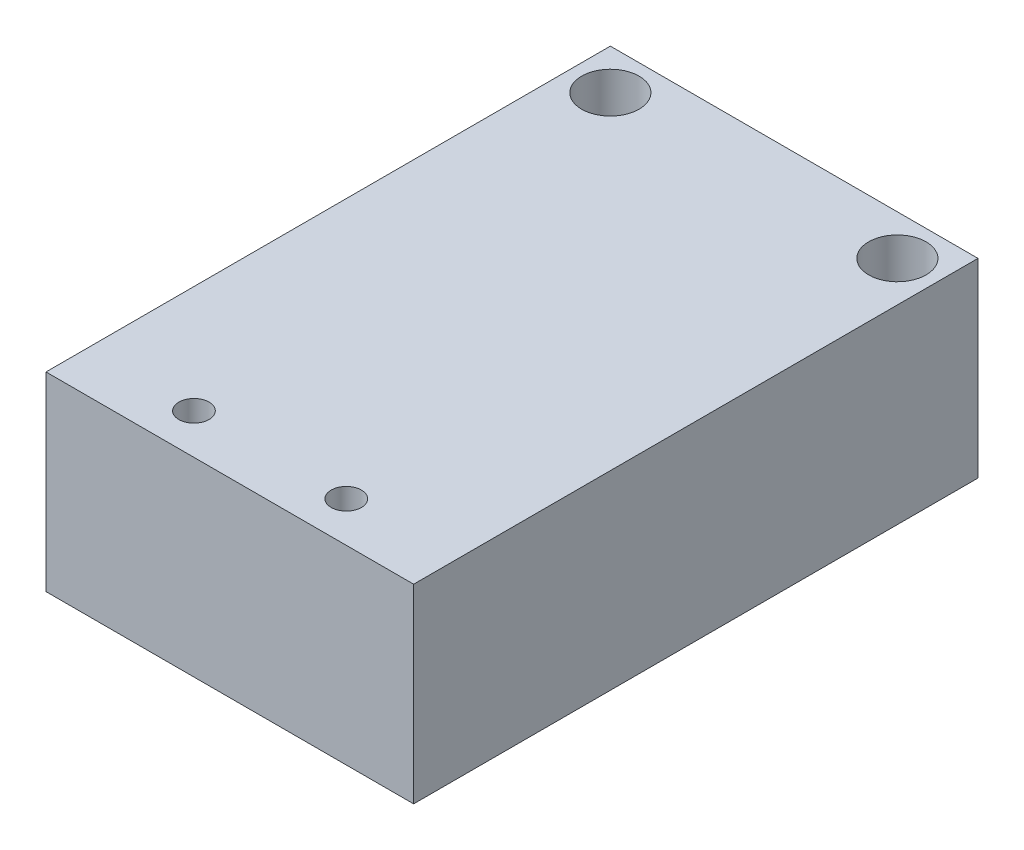
SolidWorks part; units mm, degrees
ref_plane "Front Plane" through (0, 0, 0) normal (0, 0, 1) x (1, 0, 0)
ref_plane "Top Plane" through (0, 0, 0) normal (0, 1, 0) x (1, 0, 0)
ref_plane "Right Plane" through (0, 0, 0) normal (1, 0, 0) x (0, 0, -1)
sketch "Sketch1" plane through (0, 0, 0) normal (0, 1, 0) x (1, 0, 0)
  line L1 (-7.239, -11.1125) -> (7.239, -11.1125)
  line L2 (-7.239, -11.1125) -> (-7.239, 11.1125)
  line L3 (-7.239, 11.1125) -> (7.239, 11.1125)
  line L4 (7.239, -11.1125) -> (7.239, 11.1125)
  line L5 (-7.239, -11.1125) -> (7.239, 11.1125) construction
  line L6 (-7.239, 11.1125) -> (7.239, -11.1125) construction
  point P0 (0, 0)
  dimension "D1" = 14.478
  dimension "D2" = 22.225
extrude "Boss-Extrude1" add sketch "Sketch1" along normal blind 7.493
hole_wizard "#0-80 Tapped Hole1" positions "Sketch3" profile "Sketch2" tap size "#0-80" standard "Ansi Inch" end condition through all
sketch "Sketch3" plane through (0, 7.493, 0) normal (0, 1, 0) x (-1, 0, 0)
  line L1 (7.239, 11.1125) -> (-7.239, 11.1125) construction
  point P0 (3, 9.525)
  point P1 (-3, 9.525)
  dimension "D1" = 3
  dimension "D2" = 3
  dimension "D3" = 1.5875
sketch "Sketch2" plane through (-3, 7.493, 9.525) normal (1, 0, 0) x (0, 0, 1)
  line L0 (0, 0) -> (0, 7.493)
  line L1 (0, 7.493) -> (0.5956, 7.493)
  line L2 (0.5956, 7.493) -> (0.5956, 0)
  line L5 (0.5956, 0) -> (0, 0)
  line L11 (0, -6.35) -> (0, 107.95) construction
  dimension "Thread Major Dia." = 1.1913
  dimension "Thru Tap Drill Depth" = 7.493
hole_wizard "#2 Clearance Hole1" positions "Sketch5" profile "Sketch4" hole size "#2" standard "Ansi Inch" end condition through all
sketch "Sketch5" plane through (0, 7.493, 0) normal (0, 1, 0) x (-1, 0, 0)
  line L1 (-7.239, 11.1125) -> (-7.239, -11.1125) construction
  line L2 (7.239, -11.1125) -> (7.239, 11.1125) construction
  circle A0 centre (3, 9.525) radius 0.5956 construction
  point P0 (5.6515, -9.525)
  point P1 (-5.6515, -9.525)
  dimension "D1" = 19.05
  dimension "D2" = 1.5875
  dimension "D3" = 1.5875
sketch "Sketch4" plane through (-5.6515, 7.493, -9.525) normal (1, 0, 0) x (0, 0, 1)
  line L0 (0, 0) -> (0, 7.493)
  line L1 (0, 7.493) -> (1.1303, 7.493)
  line L2 (1.1303, 7.493) -> (1.1303, 0)
  line L5 (1.1303, 0) -> (0, 0)
  line L11 (0, -6.35) -> (0, 107.95) construction
  dimension "Thru Hole Dia." = 2.2606
  dimension "Thru Hole Depth" = 7.493
hole_wizard "3/64 (0.04688) Diameter Hole1" [suppressed] positions "Sketch7" profile "Sketch6" hole size "3/64" standard "Ansi Inch"
sketch "Sketch7" plane through (0, 0, -12.7) normal (0, 0, -1) x (-1, 0, 0)
  line L0 (-7.239, 7.493) -> (-7.239, 0) construction
  line L1 (7.239, 7.493) -> (7.239, 0) construction
  point P0 (-2.9972, 3.7465)
  point P1 (2.9972, 3.7465)
  point P7 (-7.239, 3.7465)
  dimension "D1" = 4.2418
  dimension "D2" = 4.2418
sketch "Sketch6" plane through (2.9972, 3.7465, -12.7) normal (1, 0, 0) x (0, 1, 0)
  line L0 (0, 0) -> (0, 5.1202)
  line L1 (0, 5.1202) -> (0.5954, 4.7625)
  line L2 (0.5954, 4.7625) -> (0.5954, 0)
  line L5 (0.5954, 0) -> (0, 0)
  line L10 (0, 5.1202) -> (-0.5954, 4.7625) construction
  line L11 (0, -6.35) -> (0, 107.95) construction
  dimension "Hole Dia." = 1.1908
  dimension "Hole Depth" = 4.7625
  dimension "Drill Angle" = 118
sketch "Sketch8" plane through (0, 7.493, 0) normal (0, -1, 0) x (1, 0, 0)
  line L0 (-7.239, 11.1125) -> (7.239, 11.1125) construction
  line L1 (3.937, 4.7625) -> (-3.937, 4.7625)
  line L2 (3.937, 4.7625) -> (3.937, 17.4625)
  line L3 (3.937, 17.4625) -> (-3.937, 17.4625)
  line L4 (-3.937, 4.7625) -> (-3.937, 17.4625)
  line L5 (3.937, 4.7625) -> (-3.937, 17.4625) construction
  line L6 (3.937, 17.4625) -> (-3.937, 4.7625) construction
  point P0 (0, 11.1125)
  dimension "D1" = 7.874
  dimension "D2" = 12.7
extrude "Cut-Extrude1" [suppressed] cut sketch "Sketch8" along normal blind 2.032
fillet "Fillet1" [suppressed] radius 3.175
